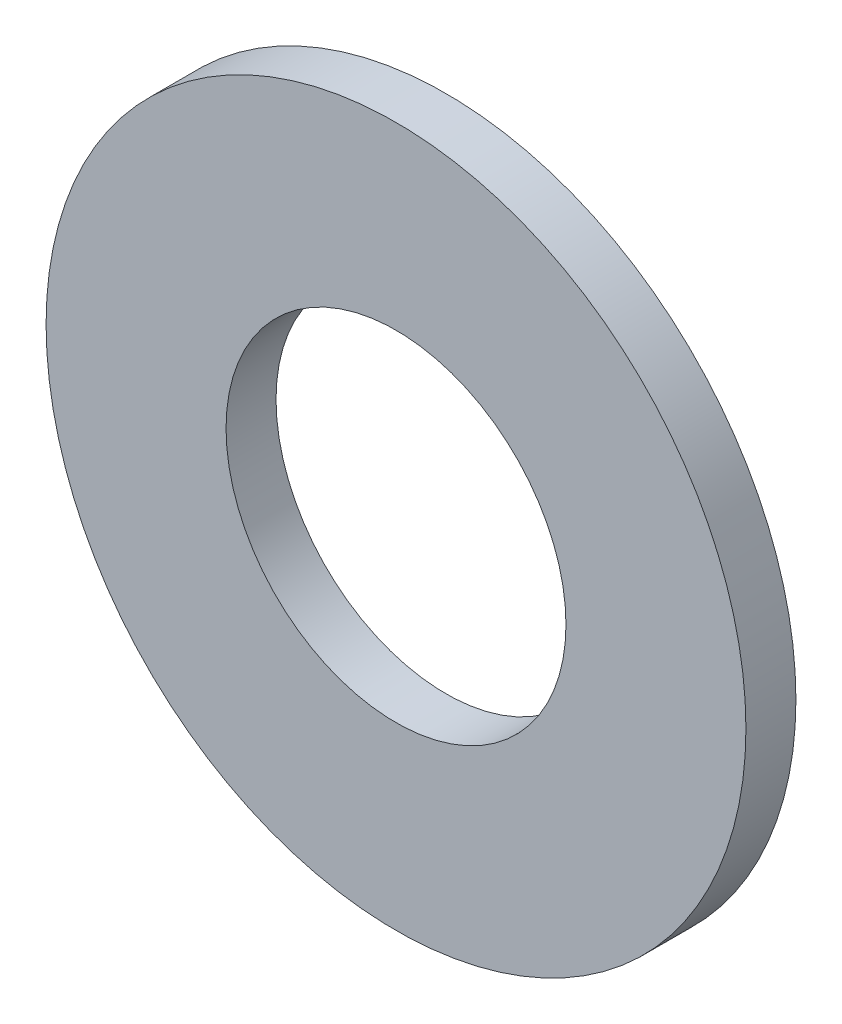
SolidWorks part; units mm, degrees
material "鉻不鏽鋼"
ref_plane "前基準面" through (0, 0, 0) normal (0, 0, 1) x (1, 0, 0)
ref_plane "上基準面" through (0, 0, 0) normal (0, 1, 0) x (1, 0, 0)
ref_plane "右基準面" through (0, 0, 0) normal (1, 0, 0) x (0, 0, -1)
sketch "草圖1" plane through (0, 0, 0) normal (0, 0, 1) x (1, 0, 0)
  circle A0 centre (0, 0) radius 3.5
  circle A1 centre (0, 0) radius 1.7
  dimension "D1" = 7
  dimension "D2" = 3.4
extrude "填料-伸長1" add sketch "草圖1" along normal mid plane 0.5
